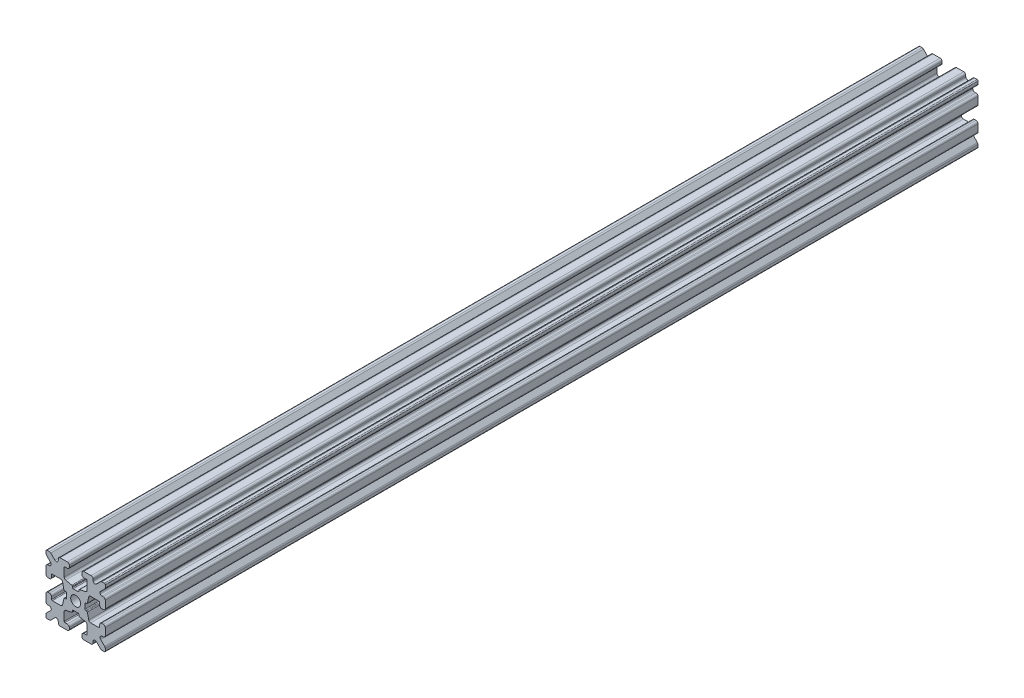
SolidWorks part; units mm, degrees
ref_plane "Front Plane" through (0, 0, 0) normal (0, 0, 1) x (1, 0, 0)
ref_plane "Top Plane" through (0, 0, 0) normal (0, 1, 0) x (1, 0, 0)
ref_plane "Right Plane" through (0, 0, 0) normal (1, 0, 0) x (0, 0, -1)
sketch "Sketch1" plane through (0, 0, 0) normal (0, 0, 1) x (1, 0, 0)
  line L1 (-7.5, -7.5) -> (7.5, -7.5)
  line L2 (-7.5, -7.5) -> (-7.5, 7.5)
  line L3 (-7.5, 7.5) -> (7.5, 7.5)
  line L4 (7.5, -7.5) -> (7.5, 7.5)
  line L5 (-7.5, -7.5) -> (7.5, 7.5) construction
  line L6 (-7.5, 7.5) -> (7.5, -7.5) construction
  circle A0 centre (0, 0) radius 1.25
  point P0 (0, 0)
  dimension "D2" = 2.5
  dimension "D1" = 15
extrude "Boss-Extrude1" add sketch "Sketch1" along normal mid plane 220.84
fillet "Fillet1" radius 0.25 4 edges at (7.5, -7.5, 0) (-7.5, -7.5, 0) (7.5, 7.5, 0) (-7.5, 7.5, 0)
sketch "Sketch2" plane through (0, 0, 110.42) normal (0, 0, 1) x (1, 0, 0)
  line L0 (-7.5, 7.25) -> (-7.5, -7.25) construction
  line L1 (-7.5, 1.6) -> (-6.1, 1.6)
  line L2 (-7.5, 1.6) -> (-7.5, -1.6)
  line L3 (-7.5, -1.6) -> (-6.1, -1.6)
  line L4 (-6.1, 1.6) -> (-6.1, 2.9)
  line L5 (0, 0) -> (-12.1036, 0) construction
  line L6 (-6.1, -2.9) -> (-3.4, -2.9)
  line L7 (0, 0) -> (-7.25, 7.25) construction
  line L8 (-6.1, 2.9) -> (-3.4, 2.9)
  line L9 (-3.4, -2.9) -> (-3.4, 2.9)
  line L10 (55, 0) -> (-55, 0) construction
  line L11 (-6.1, -2.9) -> (-6.1, -1.6)
  line L12 (2.9, 6.1) -> (1.6, 6.1)
  line L13 (2.9, 3.4) -> (-2.9, 3.4)
  line L14 (-2.9, 6.1) -> (-2.9, 3.4)
  line L15 (2.9, 6.1) -> (2.9, 3.4)
  line L16 (-1.6, 6.1) -> (-2.9, 6.1)
  line L17 (1.6, 7.5) -> (1.6, 6.1)
  line L18 (-1.6, 7.5) -> (1.6, 7.5)
  line L19 (-1.6, 7.5) -> (-1.6, 6.1)
  line L20 (-1.6, -7.5) -> (-1.6, -6.1)
  line L21 (-1.6, -7.5) -> (1.6, -7.5)
  line L22 (1.6, -7.5) -> (1.6, -6.1)
  line L23 (-1.6, -6.1) -> (-2.9, -6.1)
  line L24 (2.9, -6.1) -> (2.9, -3.4)
  line L25 (-2.9, -6.1) -> (-2.9, -3.4)
  line L26 (2.9, -3.4) -> (-2.9, -3.4)
  line L27 (2.9, -6.1) -> (1.6, -6.1)
  line L28 (6.1, -2.9) -> (6.1, -1.6)
  line L29 (3.4, -2.9) -> (3.4, 2.9)
  line L30 (6.1, 2.9) -> (3.4, 2.9)
  line L31 (6.1, -2.9) -> (3.4, -2.9)
  line L32 (6.1, 1.6) -> (6.1, 2.9)
  line L33 (7.5, -1.6) -> (6.1, -1.6)
  line L34 (7.5, 1.6) -> (7.5, -1.6)
  line L35 (7.5, 1.6) -> (6.1, 1.6)
  dimension "D1" = 3.2
  dimension "D2" = 5.8
  dimension "D3" = 1.4
  dimension "D4" = 2.7
extrude "Cut-Extrude1" cut sketch "Sketch2" against normal through all
sketch "Sketch4" plane through (0, 0, 110.42) normal (0, 0, 1) x (1, 0, 0)
  line L0 (-3.4, 2.9) -> (-2.75, 0)
  line L1 (55, 0) -> (-55, 0) construction
  line L2 (-2.75, 0) -> (-3.4, -2.9)
  line L3 (-3.4, -2.9) -> (-3.4, 2.9) construction
  line L4 (-3.4, 2.9) -> (-3.4, -2.9)
  line L5 (-2.9, 3.4) -> (0, 2.75)
  line L6 (0, 2.75) -> (2.9, 3.4)
  line L7 (2.9, 3.4) -> (-2.9, 3.4)
  line L8 (3.4, 2.9) -> (2.75, 0)
  line L9 (2.75, 0) -> (3.4, -2.9)
  line L10 (3.4, -2.9) -> (3.4, 2.9)
  line L11 (-2.9, -3.4) -> (0, -2.75)
  line L12 (0, -2.75) -> (2.9, -3.4)
  line L13 (2.9, -3.4) -> (-2.9, -3.4)
  circle A2 centre (0, 0) radius 2.75
  circle A3 centre (0, 0) radius 2.75 construction
  dimension "D1" = 1.5
extrude "Cut-Extrude3" cut sketch "Sketch4" against normal through all
fillet "Fillet3" radius 0.5 16 edges at (-6.1, -1.6, 0) (-7.5, -1.6, 0) (-6.1, 1.6, 0) (-7.5, 1.6, 0) (-1.6, -7.5, 0) (-1.6, -6.1, 0) (1.6, -7.5, 0) (1.6, -6.1, 0) (6.1, -1.6, 0) (7.5, -1.6, 0) (7.5, 1.6, 0) (6.1, 1.6, 0) (1.6, 7.5, 0) (1.6, 6.1, 0) (-1.6, 7.5, 0) (-1.6, 6.1, 0)
fillet "Fillet4" radius 0.5 8 edges at (-3.4, 2.9, 0) (-3.4, -2.9, 0) (2.9, -3.4, 0) (-2.9, -3.4, 0) (3.4, -2.9, 0) (3.4, 2.9, 0) (-2.9, 3.4, 0) (2.9, 3.4, 0)
fillet "Fillet5" radius 3 4 edges at (0, -2.75, 0) (2.75, 0, 0) (-2.75, 0, 0) (0, 2.75, 0)
fillet "Fillet6" radius 0.2 8 edges at (-2.9, -6.1, 0) (2.9, -6.1, 0) (6.1, -2.9, 0) (6.1, 2.9, 0) (2.9, 6.1, 0) (-2.9, 6.1, 0) (-6.1, -2.9, 0) (-6.1, 2.9, 0)
sketch "Sketch5" plane through (0, 0, 110.42) normal (0, 0, 1) x (1, 0, 0)
  line L0 (0, 0) -> (-7.25, 7.25) construction
  line L1 (-7.5, 6.4393) -> (-5.4607, 4.4)
  line L2 (-6.4393, 7.5) -> (-4.4, 5.4607)
  line L3 (-7.5, 4.4) -> (-5.4607, 4.4)
  line L4 (-3.8003, 2.9) -> (-5.9, 2.9) construction
  line L5 (0, 0) -> (-12.1819, 0) construction
  line L6 (-4.4, 7.5) -> (-4.4, 5.4607)
  line L7 (-2.9, 5.9) -> (-2.9, 3.8003) construction
  line L8 (-7.5, 6.4393) -> (-7.5, 4.4)
  line L9 (-7.5, 7.25) -> (-7.5, 2.1) construction
  line L10 (2.1, -7.5) -> (7.25, -7.5) construction
  line L11 (7.5, -7.25) -> (7.5, -2.1) construction
  line L12 (7.25, 7.5) -> (2.1, 7.5) construction
  line L13 (-2.1, 7.5) -> (-7.25, 7.5) construction
  line L14 (-4.4, 7.5) -> (-6.4393, 7.5)
  line L16 (55, 0) -> (-55, 0) construction
  line L17 (0, 0) -> (0, 10.993) construction
  line L18 (0, -54.6431) -> (0, 54.6431) construction
  line L20 (4.4, 7.5) -> (6.4393, 7.5)
  line L22 (7.5, 6.4393) -> (7.5, 4.4)
  line L23 (4.4, 7.5) -> (4.4, 5.4607)
  line L24 (7.5, 4.4) -> (5.4607, 4.4)
  line L25 (6.4393, 7.5) -> (4.4, 5.4607)
  line L26 (7.5, 6.4393) -> (5.4607, 4.4)
  line L27 (7.5, -6.4393) -> (5.4607, -4.4)
  line L28 (6.4393, -7.5) -> (4.4, -5.4607)
  line L29 (7.5, -4.4) -> (5.4607, -4.4)
  line L30 (4.4, -7.5) -> (4.4, -5.4607)
  line L31 (7.5, -6.4393) -> (7.5, -4.4)
  line L33 (4.4, -7.5) -> (6.4393, -7.5)
  line L36 (-4.4, -7.5) -> (-6.4393, -7.5)
  line L38 (-7.5, -6.4393) -> (-7.5, -4.4)
  line L39 (-4.4, -7.5) -> (-4.4, -5.4607)
  line L40 (-7.5, -4.4) -> (-5.4607, -4.4)
  line L41 (-6.4393, -7.5) -> (-4.4, -5.4607)
  line L42 (-7.5, -6.4393) -> (-5.4607, -4.4)
  dimension "D1" = 1.5
  dimension "D2" = 1.5
  dimension "D3" = 1.5
extrude "Cut-Extrude4" cut sketch "Sketch5" against normal through all
fillet "Fillet8" radius 0.5 24 edges at (-5.4607, 4.4, 0) (-7.5, 4.4, 0) (-5.4607, -4.4, 0) (-7.5, -4.4, 0) (-4.4, -7.5, 0) (-4.4, -5.4607, 0) (4.4, -7.5, 0) (4.4, -5.4607, 0) (5.4607, -4.4, 0) (7.5, -4.4, 0) (7.5, 4.4, 0) (5.4607, 4.4, 0) (4.4, 5.4607, 0) (4.4, 7.5, 0) (-4.4, 5.4607, 0) (-4.4, 7.5, 0) (-6.4393, 7.5, 0) (-7.5, 6.4393, 0) (6.4393, 7.5, 0) (7.5, 6.4393, 0) (6.4393, -7.5, 0) (7.5, -6.4393, 0) (-6.4393, -7.5, 0) (-7.5, -6.4393, 0)
sketch "Sketch6" plane through (0, 0, 110.42) normal (0, 0, 1) x (1, 0, 0)
  line L0 (0, 0) -> (0, 11.013) construction
  line L1 (0.6561, 2.8971) -> (2.1235, 2.8971) construction
  line L2 (0, -54.6431) -> (0, 54.6431) construction
  line L3 (0, 0) -> (7.25, 7.25) construction
  line L4 (7.5, 0.8255) -> (7.5, -0.8255)
  line L5 (2.3471, 0.8255) -> (7.5, 0.8255)
  line L6 (0, 0) -> (12.4016, 0) construction
  line L7 (0.8255, -7.5) -> (-0.8255, -7.5)
  line L8 (2.3471, -0.8255) -> (2.3471, 0.8255)
  line L9 (0.8255, -2.3471) -> (0.8255, -7.5)
  line L10 (7.5, -0.8255) -> (2.3471, -0.8255)
  line L11 (-7.5, -0.8255) -> (-2.3471, -0.8255)
  line L12 (-2.3471, -0.8255) -> (-2.3471, 0.8255)
  line L13 (-0.8255, -2.3471) -> (0.8255, -2.3471)
  line L14 (-0.8255, 7.5) -> (-0.8255, 2.3471)
  line L15 (-0.8255, 2.3471) -> (0.8255, 2.3471)
  line L16 (-0.8255, -7.5) -> (-0.8255, -2.3471)
  line L17 (0.8255, 2.3471) -> (0.8255, 7.5)
  line L18 (0.8255, 7.5) -> (-0.8255, 7.5)
  line L19 (3.9, 7.5) -> (2.1, 7.5) construction
  line L20 (-2.3471, 0.8255) -> (-7.5, 0.8255)
  line L21 (-7.5, 0.8255) -> (-7.5, -0.8255)
  point P5 (0, -2.5973)
  point P7 (0, 2.5973)
  dimension "D3" = 0.55
  dimension "D1" = 1.651
extrude "Cut-Extrude5" cut sketch "Sketch6" against normal through all
fillet "Fillet10" radius 0.2 16 edges at (-2.935, 0.8255, 0) (-2.935, -0.8255, 0) (2.935, -0.8255, 0) (2.935, 0.8255, 0) (0.8255, 2.935, 0) (-0.8255, 2.935, 0) (-2.3471, 0.8255, 0) (-2.3471, -0.8255, 0) (0.8255, 2.3471, 0) (-0.8255, 2.3471, 0) (2.3471, 0.8255, 0) (2.3471, -0.8255, 0) (0.8255, -2.935, 0) (0.8255, -2.3471, 0) (-0.8255, -2.3471, 0) (-0.8255, -2.935, 0)
